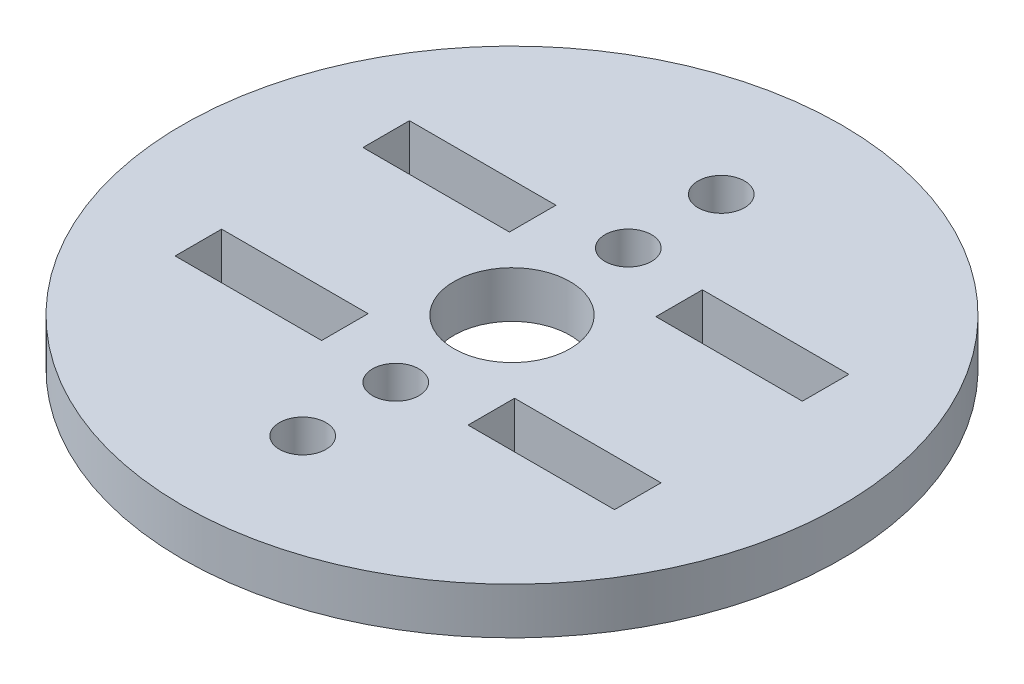
SolidWorks part; units mm, degrees
ref_plane "Alzado" through (0, 0, 0) normal (0, 0, 1) x (1, 0, 0)
ref_plane "Planta" through (0, 0, 0) normal (0, 1, 0) x (1, 0, 0)
ref_plane "Vista lateral" through (0, 0, 0) normal (1, 0, 0) x (0, 0, -1)
sketch "Croquis1" plane through (0, 0, 0) normal (0, 1, 0) x (1, 0, 0)
  line L0 (0, -1000) -> (0, 49000) construction
  line L1 (-5, -1013.8043) -> (-5, 48986.1957) construction
  line L2 (-15, 8) -> (-5, 8)
  line L3 (-15, 8) -> (-15, 4.825)
  line L4 (-15, 4.825) -> (-5, 4.825)
  line L5 (-5, 8) -> (-5, 4.825)
  line L6 (5, 8) -> (15, 8)
  line L7 (5, 8) -> (5, 4.825)
  line L8 (5, 4.825) -> (15, 4.825)
  line L9 (15, 8) -> (15, 4.825)
  line L10 (-15, -4.825) -> (-5, -4.825)
  line L11 (-15, -4.825) -> (-15, -8)
  line L12 (-15, -8) -> (-5, -8)
  line L13 (-5, -4.825) -> (-5, -8)
  line L14 (5, -4.825) -> (15, -4.825)
  line L15 (5, -4.825) -> (5, -8)
  line L16 (5, -8) -> (15, -8)
  line L17 (15, -4.825) -> (15, -8)
  line L18 (5, -1006.0612) -> (5, 48993.9388) construction
  line L19 (-1000, 0) -> (49000, 0) construction
  circle A0 centre (0, 0) radius 22.5
  circle A1 centre (0, 0) radius 3.9688
  circle A2 centre (0, 7.9375) radius 1.5875
  circle A3 centre (0, -7.9375) radius 1.5875
  circle A4 centre (0, 14.2875) radius 1.5875
  circle A5 centre (0, -14.2875) radius 1.5875
  dimension "D1" = 7.9375
  dimension "D2" = 45
  dimension "D11" = 3.175
  dimension "D12" = 3.175
  dimension "D15" = 3.175
  dimension "D16" = 3.175
  dimension "D3" = 5
  dimension "D4" = 5
  dimension "D5" = 3.175
  dimension "D6" = 3.175
  dimension "D7" = 10
  dimension "D8" = 10
  dimension "D9" = 8
  dimension "D10" = 8
  dimension "D13" = 7.9375
  dimension "D14" = 7.9375
  dimension "D17" = 14.2875
  dimension "D18" = 14.2875
extrude "Saliente-Extruir1" add sketch "Croquis1" along normal blind 3.175
